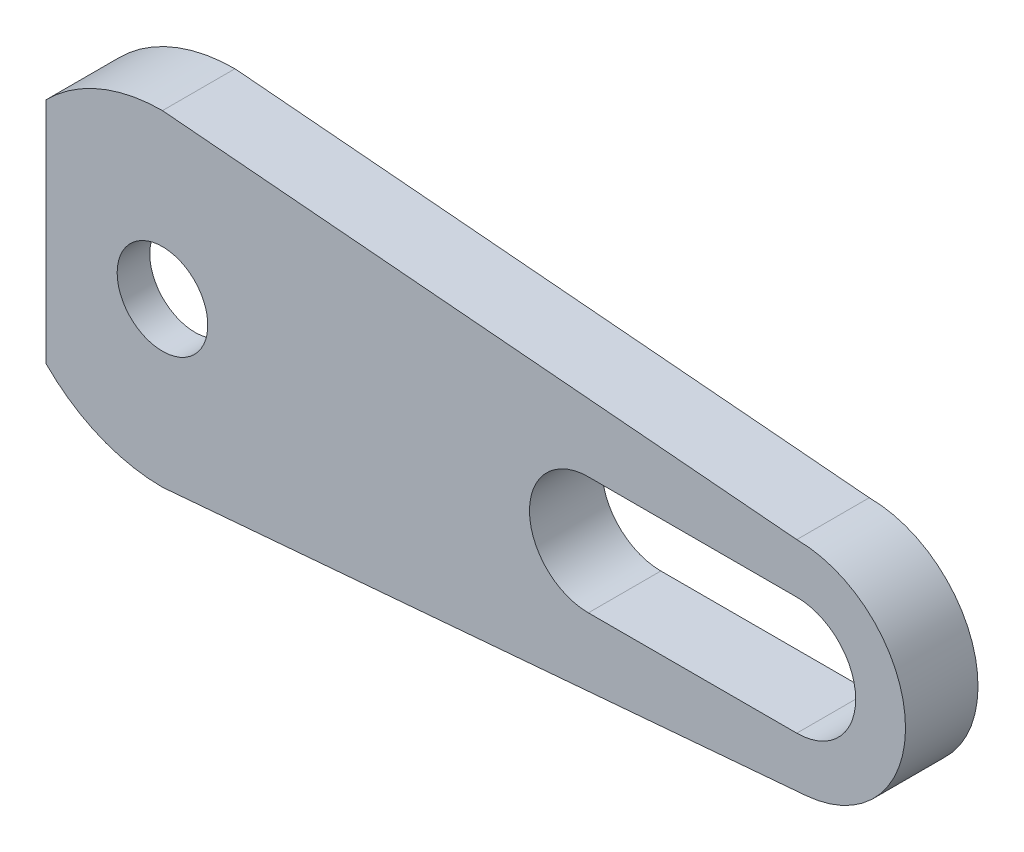
SolidWorks part; units mm, degrees
ref_plane "Front Plane" through (0, 0, 0) normal (0, 0, 1) x (1, 0, 0)
ref_plane "Top Plane" through (0, 0, 0) normal (0, 1, 0) x (1, 0, 0)
ref_plane "Right Plane" through (0, 0, 0) normal (1, 0, 0) x (0, 0, -1)
sketch "Esquisse1" plane through (0, 0, 0) normal (0, 0, 1) x (1, 0, 0)
  line L0 (-4.3758, 4.25) -> (-6.4265, 6.3008)
  line L1 (4.3758, 4.25) -> (17.3156, 2.7822)
  line L2 (17.3156, -2.7822) -> (4.3758, -4.25)
  line L3 (23.5, 3.25) -> (35, 3.25)
  line L4 (0, 9) -> (35, 6)
  line L5 (0, -9) -> (35.5087, -5.9784)
  line L6 (-4.3758, -4.25) -> (-6.4265, -6.3008)
  line L7 (23.5, -3.25) -> (35, -3.25)
  arc A0 (4.3758, 4.25) -> (-4.3758, 4.25) centre (0, 0) ccw
  arc A1 (17.3156, -2.7822) -> (17.3156, 2.7822) centre (17, 0) ccw
  arc A2 (4.3758, -4.25) -> (-4.3758, -4.25) centre (0, 0) cw
  arc A3 (-6.4265, 6.3008) -> (0, 9) centre (0, 0) cw
  arc A4 (35, 3.25) -> (35, -3.25) centre (35, 0) cw
  arc A5 (-6.4265, -6.3008) -> (0, -9) centre (0, 0) ccw
  arc A6 (35, 6) -> (35.5087, -5.9784) centre (35, 0) cw
  arc A7 (23.5, 3.25) -> (23.5, -3.25) centre (23.5, 0) ccw
  dimension "D2" = 6.1
  dimension "D3" = 2.8
  dimension "D5" = 3.25
  dimension "D6" = 9
  dimension "D8" = 35
  dimension "D1" = 8.5
  dimension "D4" = 17
  dimension "D7" = 23.5
  dimension "D9" = 6
  dimension "D10" = 11.5
extrude "Main" add sketch "Esquisse1" along normal blind 4
sketch "Esquisse2" plane through (0, 0, 4) normal (0, 0, -1) x (-1, 0, 0)
  line L0 (0, -9) -> (-13.0082, -7.8931)
  line L1 (0, -9) -> (-35.5087, -5.9784) construction
  line L2 (0, -9) -> (-35.5087, -5.9784) construction
  line L3 (0, 9) -> (-13.0082, 7.885)
  line L4 (6.4265, -6.3008) -> (6.4265, 6.3008)
  line L5 (-35, 6) -> (0, 9) construction
  line L6 (-35, 6) -> (0, 9) construction
  line L7 (0, -9) -> (-35.5087, -5.9784) construction
  line L10 (6.4265, 6.3008) -> (4.3758, 4.25) construction
  arc A0 (6.4265, 6.3008) -> (0, 9) centre (0, 0) ccw construction
  arc A1 (0, -9) -> (6.4265, -6.3008) centre (0, 0) ccw
  circle A2 centre (0, 0) radius 2.5
  arc A3 (6.4265, 6.3008) -> (0, 9) centre (0, 0) ccw
  arc A4 (-13.0082, -7.8931) -> (-13.0082, 7.885) centre (-12.332, -0.004) cw
  arc A5 (-23.5, -3.25) -> (-23.5, 3.25) centre (-23.5, 0) ccw construction
  arc A6 (0, -9) -> (6.4265, -6.3008) centre (0, 0) ccw construction
  dimension "D1" = 5
extrude "Boss-Extrude1" add sketch "Esquisse2" along normal blind 1.8
